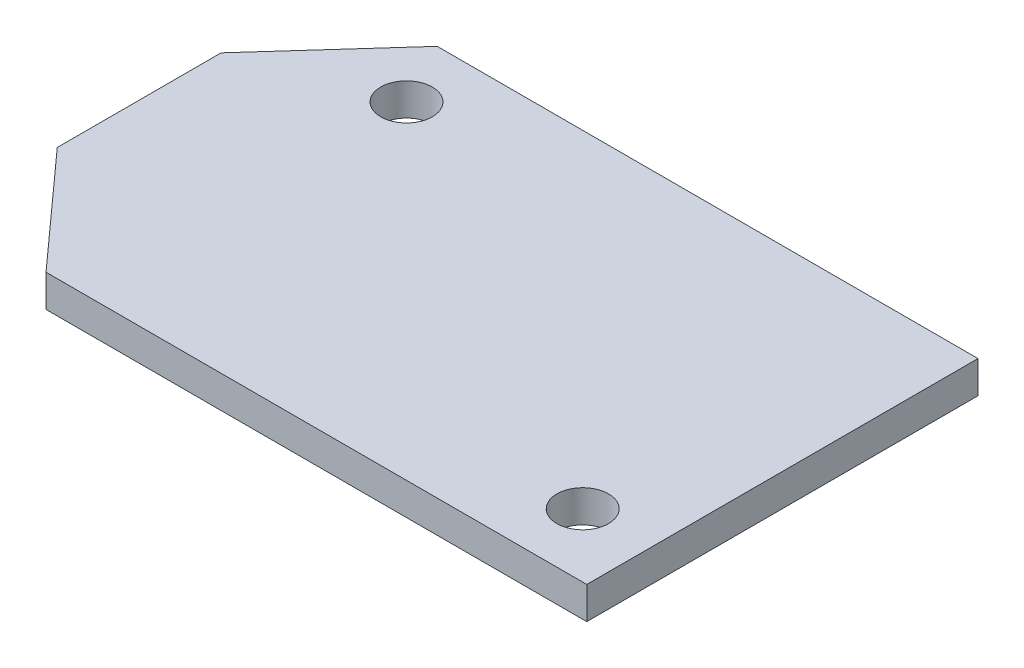
SolidWorks part; units mm, degrees
ref_plane "Front Plane" through (0, 0, 0) normal (0, 0, 1) x (1, 0, 0)
ref_plane "Top Plane" through (0, 0, 0) normal (0, 1, 0) x (1, 0, 0)
ref_plane "Right Plane" through (0, 0, 0) normal (1, 0, 0) x (0, 0, -1)
sketch "Sketch1" plane through (0, 0, 0) normal (0, 1, 0) x (1, 0, 0)
  line L0 (-23.114, 0) -> (-23.114, 21.2267) construction
  line L1 (-16.764, -12.1285) -> (16.764, -12.1285)
  line L2 (-16.764, -12.1285) -> (-16.764, 12.1285) construction
  line L3 (-16.764, 12.1285) -> (16.764, 12.1285)
  line L4 (16.764, -12.1285) -> (16.764, 12.1285)
  line L5 (-16.764, -12.1285) -> (16.764, 12.1285) construction
  line L6 (-16.764, 12.1285) -> (16.764, -12.1285) construction
  line L7 (-55, 0) -> (55, 0) construction
  line L8 (-23.114, -5.08) -> (-23.114, 5.08)
  line L9 (-23.114, 5.08) -> (-16.764, 12.1285)
  line L10 (-23.114, -5.08) -> (-16.764, -12.1285)
  circle A0 centre (12.574, -8.1915) radius 1.6
  circle A1 centre (-14.732, 8.1915) radius 1.6
  point P1 (0, 0)
  point P13 (-23.114, 0)
  point P17 (14.2202, -9.9869)
  point P18 (-14.1189, 8.8634)
  point P19 (13.5334, 12.1285)
  point P22 (13.952, -10.7999)
  point P23 (13.6677, -11.1547)
  point P24 (-16.764, 8.7486)
  dimension "D7" = 3.2
  dimension "D8" = 3.2
  dimension "D1" = 33.528
  dimension "D2" = 24.257
  dimension "D3" = 39.878
  dimension "D4" = 10.16
  dimension "D5" = 4.19
  dimension "D6" = 3.937
  dimension "D9" = 3.937
  dimension "D10" = 2.032
extrude "Boss-Extrude1" add sketch "Sketch1" along normal blind 2
